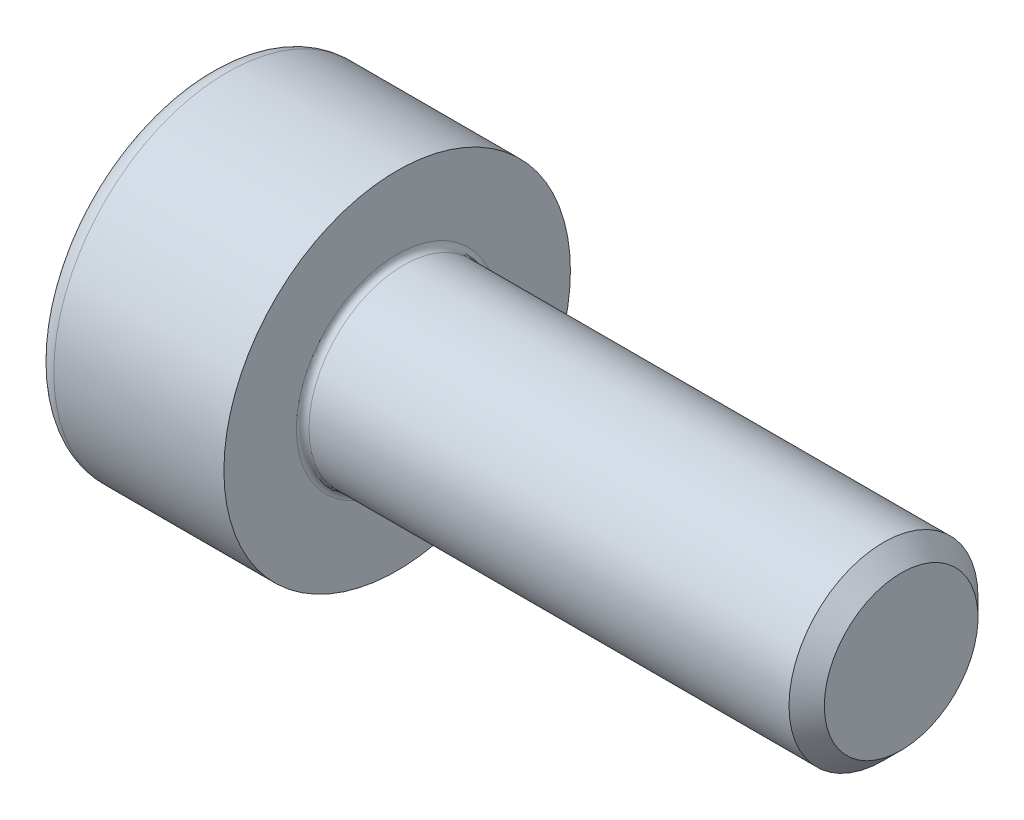
SolidWorks part; units mm, degrees
ref_plane "Plane1" through (0, 0, 0) normal (0, 0, 1) x (1, 0, 0)
ref_plane "Plane2" through (0, 0, 0) normal (0, 1, 0) x (1, 0, 0)
ref_plane "Plane3" through (0, 0, 0) normal (1, 0, 0) x (0, 0, -1)
sketch "BodySke" plane through (0, 0, 0) normal (0, 0, 1) x (1, 0, 0)
  line L0 (0, 0) -> (0, 2.75)
  line L1 (0, 2.75) -> (3, 2.75)
  line L2 (3, 2.75) -> (3, 1.5)
  line L3 (3, 1.5) -> (10.7195, 1.5)
  line L4 (11, 1.2195) -> (11, 0)
  line L5 (11, 0) -> (0, 0)
  line L6 (-31.75, 0) -> (127, 0) construction
  line L8 (11, 1.2195) -> (10.7195, 1.5)
  line L10 (11, -1.2195) -> (10.7195, -1.5) construction
  line L11 (3.5, 9.525) -> (3.5, 3.175) construction
  line L12 (3, 9.525) -> (3, 3.175) construction
  line L13 (-49, 9.525) -> (-49, 3.175) construction
  dimension "Diameter" = 3
  dimension "Head_ht" = 3
  dimension "Length" = 8
  dimension "Body_ch_ang" = 45
  dimension "Head_dia" = 5.5
  dimension "Minor_dia" = 2.439
  dimension "Advance" = 0.5
  dimension "Thread_nom" = 8
  dimension "Thread_length" = 60
revolve "Base-Revolve" add sketch "BodySke"
cosmetic thread "ThreadCosmetic"
fillet "Fillet1" radius 0.1 1 edges at (3, 0, 1.5)
fillet "Fillet2" radius 0.3 1 edges at (0, 0, 2.75)
sketch "Sketch2" plane through (0, 0, 0) normal (0, 0, 1) x (1, 0, 0)
  line L0 (0, 1.26) -> (1.3, 1.26)
  line L1 (1.3, 1.26) -> (2.0275, 0)
  line L2 (-31.75, 0) -> (127, 0) construction
  line L3 (2.0275, 0) -> (0, 0)
  line L4 (0, 0) -> (0, 1.26)
  line L6 (0, 0) -> (47.625, 0) construction
  dimension "D1" = 1.26
  dimension "D2" = 60
  dimension "Depth" = 1.3
revolve "Hex-PreBroach" cut sketch "Sketch2" angle 360 about L6
sketch "Sketch3" plane through (0, 0, 0) normal (-1, 0, 0) x (0, 0.5, 0.866)
  line L0 (0.7275, 1.26) -> (-0.7275, 1.26)
  line L1 (-0.7275, 1.26) -> (-1.4549, 0)
  line L2 (0.7275, 1.26) -> (1.4549, 0)
  line L3 (0.7275, -1.26) -> (1.4549, 0)
  line L4 (0.7275, -1.26) -> (-0.7275, -1.26)
  line L5 (-0.7275, -1.26) -> (-1.4549, 0)
  dimension "D1" = 1.26
  dimension "D2" = 1.26
  dimension "Hex_size" = 2.52
extrude "Hex" cut sketch "Sketch3" against normal blind 1.3
sketch "ThdSchSke" plane through (0, 0, 0) normal (0, 0, 1) x (1, 0, 0)
  line L0 (4.5, -1.2195) -> (4.3036, -1.5)
  line L1 (4.5, -1.2195) -> (4.6964, -1.5)
  line L2 (4.6964, -1.5) -> (4.6964, -1.875)
  line L3 (-3.175, 0) -> (5.1513, 0) construction
  line L4 (0, 2.45) -> (0, -2.45) construction
  line L5 (4.6964, -1.875) -> (4.3036, -1.875)
  line L6 (4.3036, -1.875) -> (4.3036, -1.5)
  dimension "Thread_minor" = 2.439
  dimension "Diameter" = 3
  dimension "Start" = 4.5
  dimension "SideAngle" = 55
  dimension "VeeAngle" = 70
  dimension "Overcut" = 3.75
revolve "ThreadSchematic" [suppressed] cut sketch "ThdSchSke" angle 360 about L3
pattern_linear "ThdSchPat" [suppressed]
equation "\"D2@Sketch3\" = \"Hex_size@Sketch3\" / 2"
equation "\"D1@Sketch3\" = \"Hex_size@Sketch3\" / 2"
equation "\"D1@Sketch2\" = \"Hex_size@Sketch3\" / 2"
equation "\"Thread_minor@ThreadCosmetic\"  =  \"Minor_dia@BodySke\""
equation "\"Depth@Sketch2\" =  \"Key_eng@Hex\""
equation "\"Thread_length@ThreadCosmetic\" = ((sgn( (\"Length@BodySke\" - \"Advance@BodySke\" * 3.0) - \"Thread_nom@BodySke\" )-1)*( (\"Length@BodySke\" - \"Advance@BodySke\" * 3.0) - \"Thread_nom@BodySke\" ))/-2+ \"Thread_nom@BodySke\""
equation "\"Thread_minor@ThdSchSke\" = \"Minor_dia@BodySke\""
equation "\"Diameter@ThdSchSke\" = \"Diameter@BodySke\""
equation "\"Overcut@ThdSchSke\" = \"Diameter@BodySke\" * 1.25"
equation "\"Start@ThdSchSke\" = \"Head_ht@BodySke\" + \"Length@BodySke\" - \"Thread_length@ThreadCosmetic\"  '---Non-countersunk---"
equation "\"Num_threads@ThdSchPat\" = int( \"Thread_length@ThreadCosmetic\" / \"Advance@BodySke\" + 0.999 )  + 1"
equation "\"Advance@ThdSchPat\" = \"Thread_length@ThreadCosmetic\" /  (\"Num_threads@ThdSchPat\" - 1) 'relax it"
equation "\"Num_threads@ThdSchPat\" = \"Num_threads@ThdSchPat\" - sgn( \"Num_threads@ThdSchPat\" - 1) '---chamfered tips only---"
